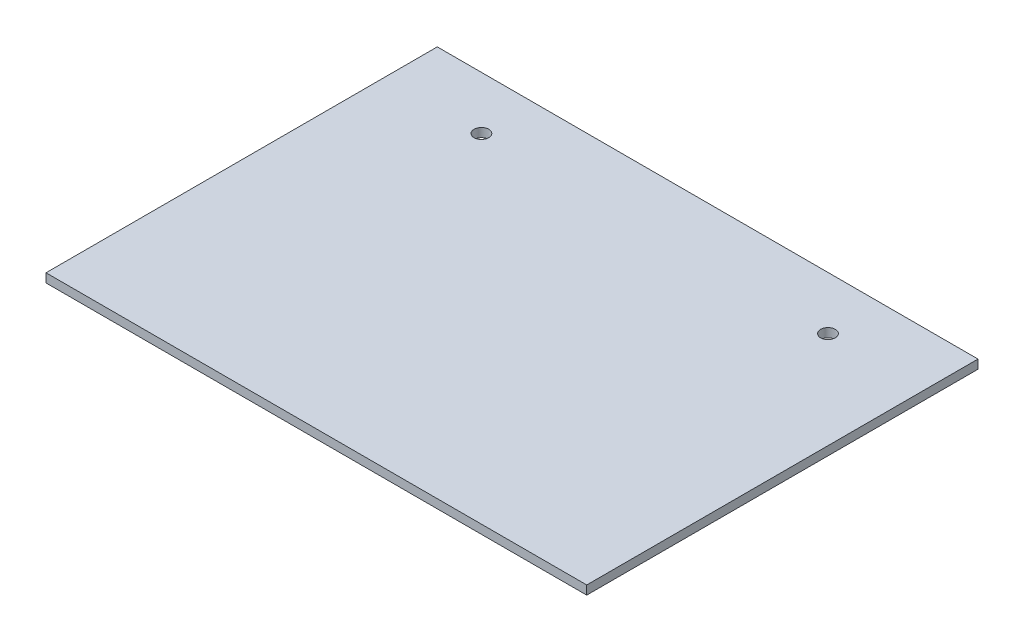
SolidWorks part; units mm, degrees
ref_plane "Front Plane" through (0, 0, 0) normal (0, 0, 1) x (1, 0, 0)
ref_plane "Top Plane" through (0, 0, 0) normal (0, 1, 0) x (1, 0, 0)
ref_plane "Right Plane" through (0, 0, 0) normal (1, 0, 0) x (0, 0, -1)
sketch "Sketch2" plane through (0, 0, 0) normal (0, 1, 0) x (1, 0, 0)
  line L0 (3, 130) -> (-180.8, 130)
  line L1 (0, 0) -> (-177.8, 0)
  line L2 (0, 0) -> (0, 127)
  line L3 (0, 127) -> (-177.8, 127)
  line L4 (-177.8, 0) -> (-177.8, 127)
  line L5 (-180.8, -3) -> (-180.8, 130)
  line L6 (3, -3) -> (-180.8, -3)
  line L7 (3, -3) -> (3, 130)
  circle A0 centre (-147.8, 112) radius 2.5
  circle A1 centre (-30, 112) radius 2.5
  dimension "D4" = 5
  dimension "D6" = 15
  dimension "D7" = 30
  dimension "D8" = 5
  dimension "D1" = 177.8
  dimension "D2" = 127
  dimension "D5" = 30
  dimension "D3" = 3
extrude "Boss-Extrude1" add sketch "Sketch2" along normal blind 3 contours L4 L1 L2 L3 A1 A0 | L6 L7 L0 L5 L1 L4 L3 L2
